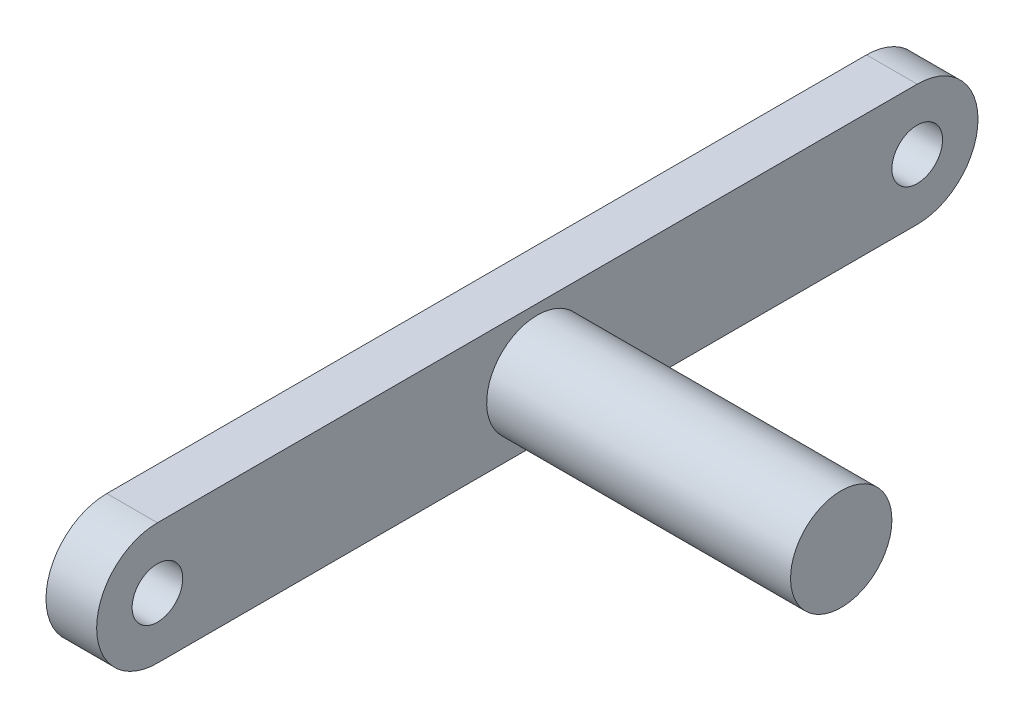
SolidWorks part; units mm, degrees
ref_plane "Plano frontal" through (0, 0, 0) normal (0, 0, 1) x (1, 0, 0)
ref_plane "Plano superior" through (0, 0, 0) normal (0, 1, 0) x (1, 0, 0)
ref_plane "Plano direito" through (0, 0, 0) normal (1, 0, 0) x (0, 0, -1)
sketch "Esboço1" plane through (0, 0, 0) normal (0, 0, 1) x (1, 0, 0)
  line L0 (0, 0) -> (0, 5)
  line L1 (0, 5) -> (30, 5)
  line L2 (30, 5) -> (30, 0)
  line L3 (30, 0) -> (0, 0)
  dimension "D1" = 5
  dimension "D2" = 30
revolve "Revolução1" add sketch "Esboço1" angle 360 about L3
sketch "Esboço2" plane through (0, 0, 0) normal (1, 0, 0) x (0, 0, -1)
  line L0 (-37.5, 0) -> (37.5, 0) construction
  line L1 (-37.5, 6) -> (37.5, 6)
  line L2 (-37.5, -6) -> (37.5, -6)
  arc A0 (-37.5, 6) -> (-37.5, -6) centre (-37.5, 0) ccw
  arc A1 (37.5, -6) -> (37.5, 6) centre (37.5, 0) ccw
  circle A2 centre (-37.5, 0) radius 2.5
  circle A3 centre (37.5, 0) radius 2.5
  point P2 (0, 0)
  dimension "D3" = 5
  dimension "D1" = 12
  dimension "D2" = 75
extrude "Ressalto-extrusão1" add sketch "Esboço2" against normal blind 5
